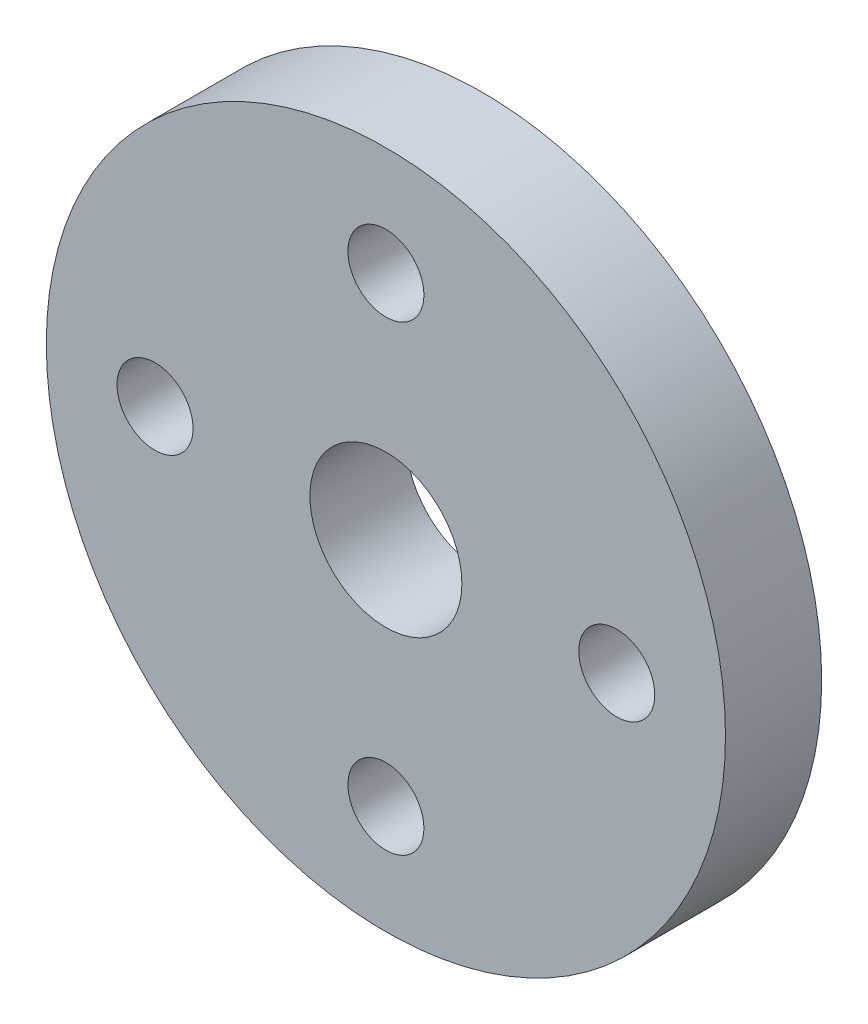
SolidWorks part; units mm, degrees
ref_plane "Front Plane" through (0, 0, 0) normal (0, 0, 1) x (1, 0, 0)
ref_plane "Top Plane" through (0, 0, 0) normal (0, 1, 0) x (1, 0, 0)
ref_plane "Right Plane" through (0, 0, 0) normal (1, 0, 0) x (0, 0, -1)
sketch "Sketch1" plane through (0, 0, 0) normal (0, 0, 1) x (1, 0, 0)
  line L0 (0, 12) -> (0, 0) construction
  line L1 (0, -0.3042) -> (0, 0) construction
  line L2 (0, 0) -> (12, 0) construction
  line L3 (0, 0) -> (0, -12) construction
  circle A0 centre (0, 0) radius 17.65
  circle A1 centre (0, 0) radius 3.95
  circle A2 centre (0, 12) radius 1.975
  circle A3 centre (12, 0) radius 1.975
  circle A4 centre (0, -12) radius 1.975
  circle A5 centre (-12, 0) radius 1.975
  point P15 (0, 0)
  dimension "D1" = 35.3
  dimension "D2" = 7.9
  dimension "D3" = 3.95
  dimension "D4" = 12
  dimension "D5" = 4
extrude "Boss-Extrude1" add sketch "Sketch1" along normal blind 5
